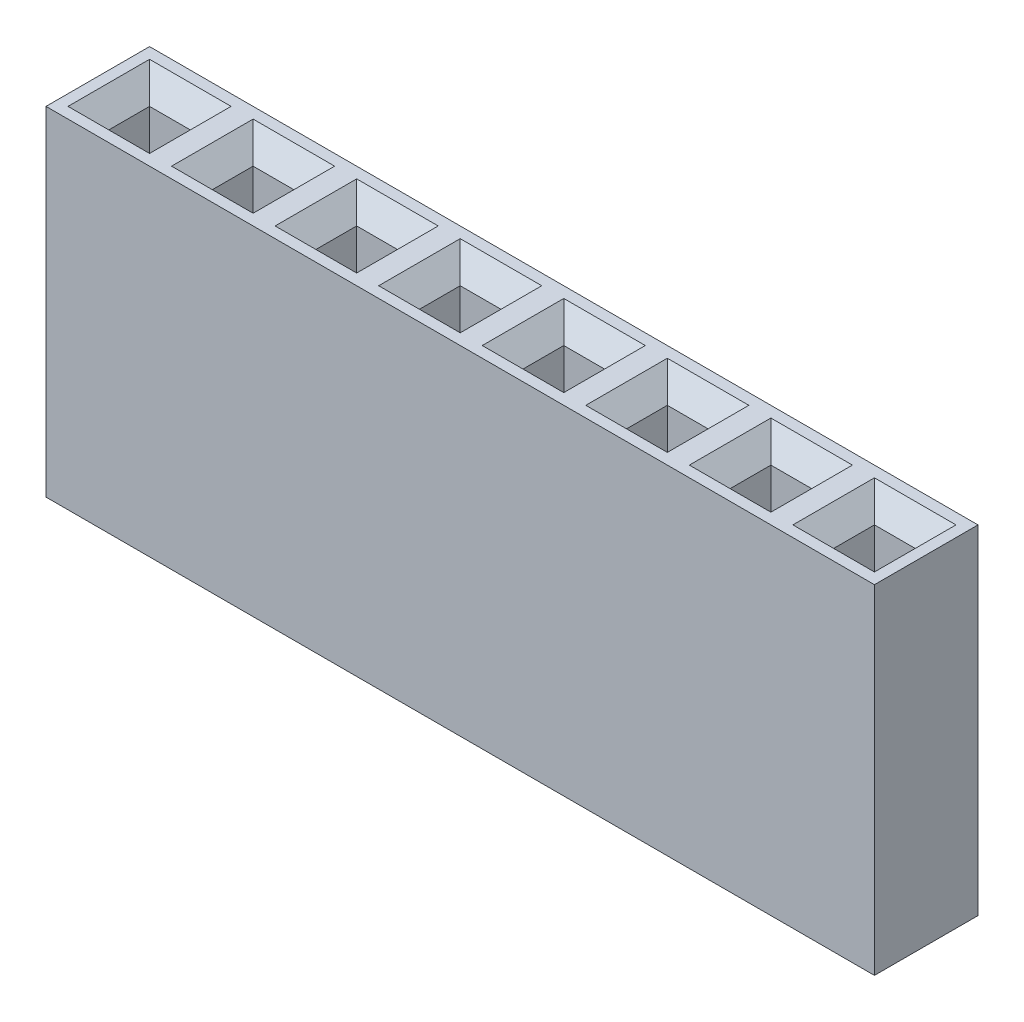
SolidWorks part; units mm, degrees
ref_plane "Front Plane" through (0, 0, 0) normal (0, 0, 1) x (1, 0, 0)
ref_plane "Top Plane" through (0, 0, 0) normal (0, 1, 0) x (1, 0, 0)
ref_plane "Right Plane" through (0, 0, 0) normal (1, 0, 0) x (0, 0, -1)
sketch "Sketch1" plane through (0, 0, 0) normal (0, 1, 0) x (1, 0, 0)
  line L0 (1.27, -1.27) -> (1.27, 1.27)
  line L1 (1.27, -1.27) -> (-1.27, -1.27)
  line L2 (1.27, 1.27) -> (-1.27, 1.27)
  line L3 (-1.27, -1.27) -> (-1.27, 1.27)
  line L4 (1.27, -1.27) -> (-1.27, 1.27) construction
  line L5 (1.27, 1.27) -> (-1.27, -1.27) construction
  point P1 (0, 0)
  dimension "D1" = 2.54
  dimension "D2" = 2.54
extrude "Boss-Extrude1" add sketch "Sketch1" along normal blind 8.3
sketch "Sketch2" plane through (0, 8.3, 0) normal (0, 1, 0) x (-1, 0, 0)
  line L0 (-0.5, 0.5) -> (-0.5, -0.5)
  line L1 (-0.5, 0.5) -> (0.5, 0.5)
  line L2 (-0.5, -0.5) -> (0.5, -0.5)
  line L3 (0.5, 0.5) -> (0.5, -0.5)
  line L4 (-0.5, 0.5) -> (0.5, -0.5) construction
  line L5 (-0.5, -0.5) -> (0.5, 0.5) construction
  point P1 (0, 0)
  dimension "D1" = 1
  dimension "D2" = 1
extrude "Cut-Extrude1" cut sketch "Sketch2" against normal blind 4
chamfer "Chamfer1" distance 0.5 angle 45 4 edges at (0, 8.3, 0.5) (0.5, 8.3, 0) (0, 8.3, -0.5) (-0.5, 8.3, 0)
pattern_linear "LPattern1" count 8 spacing 2.54 along (1, 0, 0) of "Boss-Extrude1", "Cut-Extrude1", "Chamfer1"
